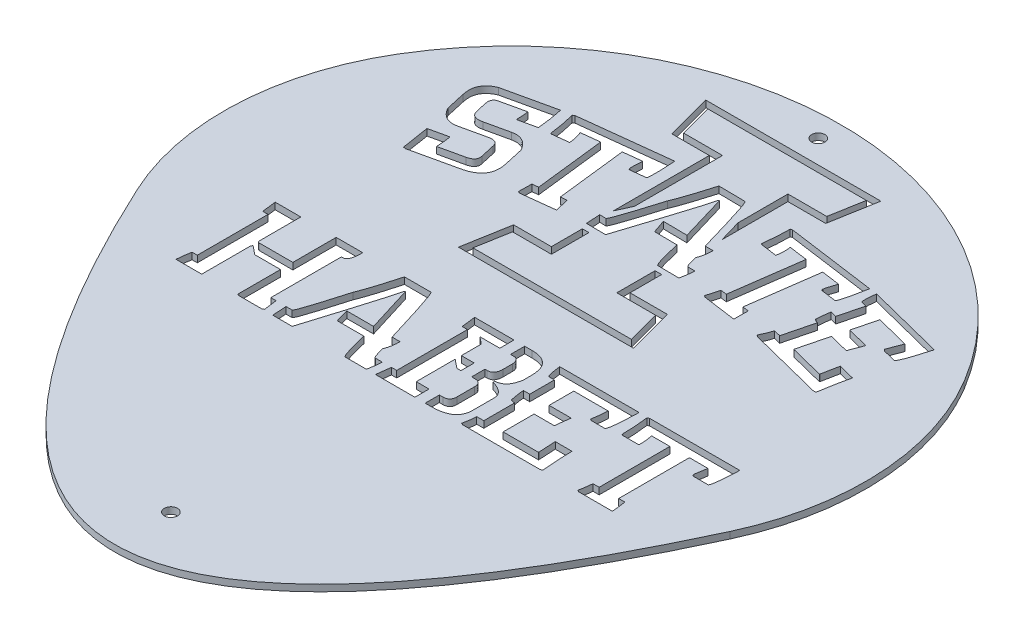
SolidWorks part; units mm, degrees
ref_plane "Front Plane" through (0, 0, 0) normal (0, 0, 1) x (1, 0, 0)
ref_plane "Top Plane" through (0, 0, 0) normal (0, 1, 0) x (1, 0, 0)
ref_plane "Right Plane" through (0, 0, 0) normal (1, 0, 0) x (0, 0, -1)
sketch "Sketch1" plane through (0, 0, 0) normal (0, 1, 0) x (1, 0, 0)
  arc A1 (105.41, 0) -> (-21.59, 0) centre (41.91, 0) ccw
  spline S0 degree 2 poles (-21.59, 0) (41.91, -152.4) (105.41, 0) knots 0 0 0 1 1 1
  dimension "D1" = 63.5
extrude "Boss-Extrude1" add sketch "Sketch1" along normal blind 1.27
fillet "Fillet1" radius 50.8 2 edges at (105.41, 0.635, 0) (-21.59, 0.635, 0)
sketch "Sketch2" plane through (0, 1.27, 0) normal (0, 1, 0) x (1, 0, 0)
  line L0 (-19.7843, 6.5271) -> (103.6043, 6.5271) construction
  line L1 (0.3218, -3.7763) -> (5.2567, -3.7763)
  line L2 (5.2567, -3.7763) -> (5.2567, -11.77)
  line L3 (5.5918, -12.105) -> (12.0561, -12.105)
  line L4 (12.0561, -12.105) -> (12.0561, -3.7763)
  line L5 (12.0561, -3.7763) -> (17.1645, -3.7763)
  line L6 (16.1396, -6.5039) -> (15.8085, -6.5039)
  line L7 (15.8085, -6.5039) -> (15.8085, -20.0987)
  line L8 (15.8085, -20.0987) -> (16.8176, -20.0987)
  line L9 (17.1645, -22.6529) -> (16.8176, -22.8263)
  line L10 (16.8176, -22.8263) -> (12.403, -22.8263)
  line L11 (12.0561, -22.4794) -> (12.0561, -14.4857)
  line L12 (12.0561, -14.4857) -> (7.1211, -14.4857)
  line L13 (7.1211, -14.4857) -> (5.4302, -13.1298)
  line L14 (5.4302, -13.1298) -> (5.2567, -13.4727)
  line L15 (5.2567, -13.4727) -> (5.2567, -22.8263)
  line L16 (5.2567, -22.8263) -> (0.3218, -22.8263)
  line L17 (0.6687, -20.0987) -> (1.6777, -20.0987)
  line L18 (1.6777, -20.0987) -> (1.6777, -6.5039)
  line L19 (1.6777, -6.5039) -> (0.6687, -6.5039)
  line L20 (25.2015, -3.7881) -> (30.298, -3.7881)
  line L21 (34.0347, -15.0021) -> (35.5641, -15.0021)
  line L22 (35.5641, -15.0021) -> (35.5641, -15.1755)
  line L23 (35.911, -20.1105) -> (37.2669, -20.1105)
  line L24 (36.924, -22.8263) -> (32.8522, -22.8263)
  line L25 (31.1494, -17.5563) -> (26.0529, -17.5563)
  line L26 (25.3631, -15.0021) -> (30.4715, -15.0021)
  line L27 (30.4715, -15.0021) -> (27.7439, -6.1689)
  line L28 (27.7439, -6.1689) -> (27.5822, -6.1689)
  line L29 (22.6473, -22.8263) -> (18.9106, -22.8263)
  line L30 (18.9106, -22.8263) -> (18.9106, -22.6529)
  line L31 (18.7372, -20.1105) -> (19.9197, -20.1105)
  line L32 (38.6662, -3.7763) -> (46.2361, -3.7763)
  line L33 (53.8061, -8.0333) -> (53.8061, -9.5626)
  line L34 (51.2519, -12.4479) -> (51.2519, -12.7948)
  line L35 (53.9795, -15.3371) -> (53.9795, -19.4207)
  line L36 (49.3875, -22.8263) -> (48.2132, -22.8263)
  line L37 (39.013, -20.0987) -> (40.0221, -20.0987)
  line L38 (40.0221, -20.0987) -> (40.0221, -6.5039)
  line L39 (40.0221, -6.5039) -> (39.013, -6.5039)
  line L40 (43.7746, -7.6864) -> (43.7746, -11.427)
  line L41 (43.7746, -11.427) -> (46.2361, -11.427)
  line L42 (50.0654, -9.7242) -> (50.0654, -7.8598)
  line L43 (49.214, -6.5039) -> (48.3, -6.5039)
  line L44 (43.7746, -12.6213) -> (43.7746, -20.0987)
  line L45 (43.7746, -20.0987) -> (46.2361, -20.0987)
  line L46 (50.227, -18.7427) -> (50.227, -15.3371)
  line L47 (48.8711, -13.9812) -> (48.3, -13.9812)
  line L48 (45.4655, -13.9812) -> (43.7746, -12.6213)
  line L49 (55.0634, -3.8157) -> (70.3373, -3.8157)
  line L50 (69.6554, -9.7637) -> (67.117, -9.7637)
  line L51 (67.117, -9.7637) -> (66.7701, -9.5902)
  line L52 (67.117, -6.5315) -> (60.4911, -6.5315)
  line L53 (60.4911, -6.5315) -> (60.4911, -11.2772)
  line L54 (60.4911, -11.2772) -> (64.7363, -11.2772)
  line L55 (64.4012, -14.1665) -> (60.4911, -14.1665)
  line L56 (60.4911, -14.1665) -> (60.4911, -20.1105)
  line L57 (60.4911, -20.1105) -> (67.2904, -20.1105)
  line L58 (67.2904, -20.1105) -> (67.2904, -19.941)
  line L59 (67.117, -16.7207) -> (70.3373, -16.7207)
  line L60 (70.6803, -22.6529) -> (70.3373, -22.8263)
  line L61 (70.3373, -22.8263) -> (55.4103, -22.8263)
  line L62 (55.4103, -22.8263) -> (55.0634, -22.6529)
  line L63 (55.4103, -20.1105) -> (56.7662, -20.1105)
  line L64 (56.7662, -20.1105) -> (56.7662, -14.1665)
  line L65 (55.568, -11.2772) -> (56.7662, -11.2772)
  line L66 (56.7662, -11.2772) -> (56.7662, -6.5315)
  line L67 (56.7662, -6.5315) -> (55.7414, -6.5315)
  line L68 (72.3121, -3.7763) -> (89.6593, -3.7763)
  line L69 (88.9813, -9.2158) -> (86.2537, -9.2158)
  line L70 (86.2537, -6.5039) -> (82.6865, -6.5039)
  line L71 (82.6865, -6.5039) -> (82.6865, -20.0987)
  line L72 (82.6865, -20.0987) -> (83.873, -20.0987)
  line L73 (84.2159, -22.8263) -> (77.7516, -22.8263)
  line L74 (77.7516, -22.8263) -> (77.4047, -22.6529)
  line L75 (77.7516, -20.0987) -> (78.938, -20.0987)
  line L76 (78.938, -20.0987) -> (78.938, -6.5039)
  line L77 (78.938, -6.5039) -> (75.3708, -6.5039)
  line L78 (75.7019, -9.2158) -> (72.6432, -9.2158)
  line L79 (71.9652, -3.9497) -> (72.3121, -3.7763)
  line L80 (46.2361, -6.5039) -> (42.4029, -6.5039)
  line L82 (46.2361, -20.0987) -> (46.2361, -22.8263)
  line L84 (48.2132, -20.0987) -> (48.2132, -22.8263)
  line L86 (48.3, -13.9812) -> (48.3, -11.427)
  line L88 (46.2361, -13.9812) -> (46.2361, -11.427)
  line L90 (48.3, -6.5039) -> (48.3, -3.7763)
  line L92 (46.2361, -6.5039) -> (46.2361, -3.7763)
  line L93 (48.3, -11.427) -> (48.6977, -11.427)
  line L94 (46.2361, -13.9812) -> (45.4655, -13.9812)
  line L95 (48.2132, -20.0987) -> (48.8711, -20.0987)
  line L96 (46.2361, -22.8263) -> (38.6662, -22.8263)
  line L97 (48.3, -3.7763) -> (49.7225, -3.7763)
  arc A0 (-12.5617, 32.6356) -> (-15.0576, -14.8714) centre (31.0157, 6.5271) ccw construction
  arc A1 (98.8776, -14.8714) -> (96.3817, 32.6356) centre (52.8043, 6.5271) ccw construction
  spline S0 degree 3 poles (5.2567, -11.77) (5.2767, -11.8548) (5.3249, -12.0461) (5.5115, -12.11) (5.5918, -12.105) knots 0 0 0 0 0.531818 1 1 1 1
  spline S1 degree 3 poles (17.1645, -3.7763) (17.1601, -4.1742) (17.1498, -4.7348) (17.0306, -5.4153) (16.9262, -5.8056) (16.7819, -6.1098) (16.5581, -6.4058) (16.3037, -6.5067) (16.1396, -6.5039) knots 0 0 0 0 0.377825 0.528227 0.653888 0.759096 0.845794 1 1 1 1
  spline S2 degree 3 poles (16.8176, -20.0987) (16.814, -20.2059) (16.8417, -20.3915) (16.8635, -20.6762) (16.9085, -20.9683) (16.9512, -21.3148) (17.0487, -21.8808) (17.1036, -22.3353) (17.1645, -22.6529) knots 0 0 0 0 0.124228 0.21791 0.332039 0.467782 0.624075 1 1 1 1
  spline S3 degree 3 poles (12.403, -22.8263) (12.318, -22.8238) (12.0973, -22.785) (12.0586, -22.5644) (12.0561, -22.4794) knots 0 0 0 0 0.5 1 1 1 1
  spline S4 degree 3 poles (0.3218, -22.8263) (0.3165, -22.6719) (0.3428, -22.4242) (0.367, -22.0674) (0.4109, -21.7462) (0.4547, -21.3854) (0.5491, -20.8333) (0.6074, -20.3977) (0.6687, -20.0987) knots 0 0 0 0 0.167857 0.271329 0.389634 0.521087 0.667537 1 1 1 1
  spline S5 degree 3 poles (0.6687, -6.5039) (0.6085, -6.144) (0.554, -5.6333) (0.4561, -5.0015) (0.4132, -4.6261) (0.3683, -4.3196) (0.3476, -4.0427) (0.3199, -3.8703) (0.3218, -3.7763) knots 0 0 0 0 0.397879 0.560026 0.697261 0.809965 0.897811 1 1 1 1
  spline S6 degree 3 poles (30.298, -3.7881) (30.3661, -3.8248) (30.4363, -3.9693) (30.5488, -4.2076) (30.6729, -4.5173) (30.8211, -4.9121) (31.001, -5.3927) (31.1939, -5.9635) (31.4172, -6.6196) (31.6586, -7.3647) (31.9339, -8.1958) (32.2222, -9.117) (32.5383, -10.1249) (32.8826, -11.2182) (33.3801, -12.8553) (33.7761, -14.1233) (34.0347, -15.0021) knots 0 0 0 0 0.018773 0.039327 0.067393 0.103006 0.146294 0.197354 0.255675 0.321893 0.395795 0.477496 0.566465 0.663438 0.767898 1 1 1 1
  spline S7 degree 3 poles (35.5641, -15.1755) (35.5648, -15.6483) (35.4856, -16.5757) (35.2298, -17.4708) (35.0596, -17.8913) knots 0 0 0 0 0.510454 1 1 1 1
  spline S8 degree 3 poles (35.0596, -17.8913) (35.1356, -18.2179) (35.265, -18.6679) (35.4319, -19.2222) (35.5425, -19.5348) (35.6415, -19.7812) (35.7482, -19.979) (35.8327, -20.0977) (35.911, -20.1105) knots 0 0 0 0 0.415941 0.581563 0.718283 0.827951 0.909707 1 1 1 1
  spline S9 degree 3 poles (37.2669, -20.1105) (37.2681, -20.2619) (37.2542, -20.5079) (37.2195, -20.8611) (37.1787, -21.1828) (37.1326, -21.5418) (37.0487, -22.094) (36.9742, -22.5255) (36.924, -22.8263) knots 0 0 0 0 0.165637 0.269704 0.388543 0.520588 0.666057 1 1 1 1
  spline S10 degree 3 poles (32.8522, -22.8263) (32.7974, -22.8218) (32.728, -22.7534) (32.646, -22.6308) (32.5693, -22.4841) (32.4826, -22.2993) (32.392, -22.0729) (32.2997, -21.8048) (32.1962, -21.4963) (32.0873, -21.1463) (31.9675, -20.7556) (31.8466, -20.3229) (31.7207, -19.8481) (31.5875, -19.3329) (31.39, -18.5657) (31.2491, -17.9676) (31.1494, -17.5563) knots 0 0 0 0 0.0276 0.04989 0.079536 0.116114 0.159439 0.210268 0.268221 0.333986 0.406901 0.487456 0.574996 0.670392 0.772966 1 1 1 1
  spline S11 degree 3 poles (26.0529, -17.5563) (25.9507, -17.2492) (25.803, -16.8139) (25.6343, -16.2609) (25.5398, -15.9174) (25.4647, -15.6218) (25.3956, -15.324) (25.3673, -15.1214) (25.3631, -15.0021) knots 0 0 0 0 0.366212 0.519992 0.654155 0.76917 0.86511 1 1 1 1
  spline S12 degree 3 poles (27.5822, -6.1689) (27.5828, -6.2184) (27.5635, -6.3058) (27.5384, -6.4429) (27.5002, -6.5892) (27.458, -6.7655) (27.4069, -6.9722) (27.3423, -7.2079) (27.2736, -7.4756) (27.1882, -7.7715) (27.1001, -8.0984) (26.995, -8.4534) (26.8863, -8.8405) (26.7635, -9.2564) (26.6327, -9.7029) (26.4967, -10.1795) (26.3445, -10.6843) (26.1893, -11.2202) (26.0173, -11.784) (25.8417, -12.3801) (25.6515, -13.0048) (25.4552, -13.6611) (25.2458, -14.3451) (25.0283, -15.0596) (24.8053, -15.8042) (24.5675, -16.5789) (24.3188, -17.3821) (24.0691, -18.2184) (23.797, -19.0792) (23.5278, -19.9756) (23.1441, -21.2281) (22.8431, -22.18) (22.6473, -22.8263) knots 0 0 0 0 0.008482 0.015422 0.024059 0.034567 0.046726 0.060811 0.076767 0.094434 0.113971 0.13522 0.158339 0.183391 0.210094 0.238665 0.268953 0.301108 0.33498 0.370721 0.408395 0.44772 0.488979 0.531889 0.576668 0.623164 0.671811 0.721826 0.773842 0.827659 0.88341 1 1 1 1
  spline S13 degree 3 poles (18.9106, -22.6529) (18.8851, -22.3323) (18.852, -21.8788) (18.8041, -21.3103) (18.7827, -20.9658) (18.7605, -20.6756) (18.7479, -20.397) (18.7397, -20.2143) (18.7372, -20.1105) knots 0 0 0 0 0.378522 0.535222 0.671642 0.784811 0.877726 1 1 1 1
  spline S14 degree 3 poles (19.9197, -20.1105) (19.9851, -20.0698) (20.0578, -19.9407) (20.163, -19.7297) (20.2745, -19.475) (20.3918, -19.1515) (20.5362, -18.7653) (20.6926, -18.3115) (20.8651, -17.7922) (21.0556, -17.2065) (21.2589, -16.5543) (21.4791, -15.8351) (21.7216, -15.0521) (21.9723, -14.1998) (22.3414, -12.9306) (22.6318, -11.9467) (22.8207, -11.2654) knots 0 0 0 0 0.02398 0.046649 0.076156 0.113186 0.157286 0.208717 0.26749 0.333211 0.40669 0.487124 0.575043 0.670203 0.772728 1 1 1 1
  spline S15 degree 3 poles (22.8207, -11.2654) (22.9937, -10.8713) (23.2405, -10.2161) (23.5681, -9.2626) (23.8563, -8.384) (24.1602, -7.3918) (24.6266, -5.8518) (24.9663, -4.6357) (25.2015, -3.7881) knots 0 0 0 0 0.16438 0.267414 0.385207 0.517635 0.663905 1 1 1 1
  spline S16 degree 3 poles (49.7225, -3.7763) (50.0428, -3.7745) (50.5096, -3.805) (51.1038, -3.9183) (51.5047, -4.0313) (51.8741, -4.1812) (52.2107, -4.3676) (52.5166, -4.5854) (52.7917, -4.8359) (53.0333, -5.1205) (53.2377, -5.4407) (53.4187, -5.7885) (53.5573, -6.1755) (53.6734, -6.5925) (53.7784, -7.2144) (53.8067, -7.6999) (53.8061, -8.0333) knots 0 0 0 0 0.141988 0.206643 0.267847 0.326362 0.382935 0.43805 0.49247 0.547434 0.603008 0.660577 0.72084 0.784848 0.852262 1 1 1 1
  spline S17 degree 3 poles (53.8061, -9.5626) (53.7298, -9.9914) (53.5818, -10.6017) (53.2325, -11.3128) (52.9356, -11.728) (52.587, -12.053) (52.0419, -12.366) (51.5697, -12.4538) (51.2519, -12.4479) knots 0 0 0 0 0.309204 0.44026 0.558794 0.668748 0.775024 1 1 1 1
  spline S18 degree 3 poles (51.2519, -12.7948) (51.6605, -12.9151) (52.2378, -13.1195) (52.9065, -13.5074) (53.2957, -13.8127) (53.6042, -14.1462) (53.8955, -14.6383) (53.9799, -15.0591) (53.9795, -15.3371) knots 0 0 0 0 0.318967 0.454552 0.576178 0.687424 0.792188 1 1 1 1
  spline S19 degree 3 poles (53.9795, -19.4207) (53.9753, -19.6869) (53.9498, -20.0798) (53.8269, -20.5756) (53.6987, -20.9111) (53.539, -21.2204) (53.3361, -21.4994) (53.1058, -21.7574) (52.8316, -21.9836) (52.5256, -22.1848) (52.1794, -22.3534) (51.8039, -22.5047) (51.3882, -22.6202) (50.9398, -22.7171) (50.2686, -22.7966) (49.7474, -22.8338) (49.3875, -22.8263) knots 0 0 0 0 0.122782 0.180144 0.234516 0.287818 0.339851 0.39295 0.446621 0.502992 0.561152 0.623604 0.689077 0.759544 0.834572 1 1 1 1
  spline S20 degree 3 poles (38.6662, -22.8263) (38.6643, -22.7322) (38.692, -22.5598) (38.7127, -22.283) (38.7576, -21.9764) (38.8005, -21.6011) (38.8984, -20.9693) (38.9529, -20.4586) (39.013, -20.0987) knots 0 0 0 0 0.102189 0.190035 0.302739 0.439974 0.602121 1 1 1 1
  spline S21 degree 3 poles (39.013, -6.5039) (38.9529, -6.144) (38.8984, -5.6333) (38.8005, -5.0015) (38.7576, -4.6261) (38.7127, -4.3196) (38.692, -4.0427) (38.6643, -3.8703) (38.6662, -3.7763) knots 0 0 0 0 0.397879 0.560026 0.697261 0.809965 0.897811 1 1 1 1
  spline S22 degree 3 poles (42.4029, -6.5039) (42.6032, -6.6581) (42.8861, -6.8721) (43.2248, -7.1508) (43.4196, -7.3116) (43.5694, -7.445) (43.6894, -7.5609) (43.7619, -7.6346) (43.7746, -7.6864) knots 0 0 0 0 0.416958 0.584812 0.72325 0.833736 0.914955 1 1 1 1
  spline S23 degree 3 poles (48.6977, -11.427) (48.8988, -11.4228) (49.2012, -11.3894) (49.5355, -11.1952) (49.7353, -11.005) (49.8856, -10.7568) (50.0347, -10.3315) (50.0693, -9.9745) (50.0654, -9.7242) knots 0 0 0 0 0.245182 0.352852 0.460208 0.573842 0.698393 1 1 1 1
  spline S24 degree 3 poles (50.0654, -7.8598) (50.0669, -7.7141) (50.0443, -7.4989) (49.9527, -7.2319) (49.8564, -7.0536) (49.7373, -6.889) (49.534, -6.6877) (49.3478, -6.57) (49.214, -6.5039) knots 0 0 0 0 0.257766 0.378193 0.496611 0.614573 0.73607 1 1 1 1
  spline S25 degree 3 poles (48.8711, -20.0987) (49.0734, -20.1057) (49.359, -20.0623) (49.7013, -19.9222) (49.8942, -19.7657) (50.0507, -19.5713) (50.1967, -19.2309) (50.2299, -18.9423) (50.227, -18.7427) knots 0 0 0 0 0.274588 0.390158 0.499896 0.609633 0.72757 1 1 1 1
  spline S26 degree 3 poles (50.227, -15.3371) (50.2277, -15.1371) (50.1995, -14.8464) (50.0495, -14.5079) (49.8944, -14.3138) (49.7003, -14.1588) (49.3618, -14.0088) (49.0712, -13.9805) (48.8711, -13.9812) knots 0 0 0 0 0.274057 0.390311 0.5 0.609689 0.725943 1 1 1 1
  spline S27 degree 3 poles (70.3373, -3.8157) (70.3212, -4.2808) (70.3024, -4.9551) (70.2641, -5.8221) (70.2332, -6.403) (70.1965, -6.9376) (70.1631, -7.4266) (70.1222, -7.8679) (70.0847, -8.2624) (70.041, -8.6107) (69.9956, -8.9134) (69.9435, -9.1694) (69.8952, -9.3796) (69.8404, -9.5424) (69.778, -9.6803) (69.7141, -9.7597) (69.6554, -9.7637) knots 0 0 0 0 0.230352 0.333856 0.429597 0.518237 0.599091 0.672218 0.737577 0.795252 0.845932 0.889041 0.924531 0.952707 0.973649 1 1 1 1
  spline S28 degree 3 poles (66.7701, -9.5902) (66.8245, -9.232) (66.897, -8.7211) (66.9825, -8.0731) (67.0278, -7.6654) (67.0696, -7.3084) (67.1029, -6.9367) (67.118, -6.6829) (67.117, -6.5315) knots 0 0 0 0 0.352909 0.50259 0.636562 0.752444 0.852662 1 1 1 1
  spline S29 degree 3 poles (64.7363, -11.2772) (64.683, -11.6248) (64.6182, -12.1206) (64.5329, -12.7445) (64.4846, -13.1321) (64.4506, -13.4661) (64.4151, -13.8045) (64.4008, -14.0322) (64.4012, -14.1665) knots 0 0 0 0 0.362431 0.515491 0.649224 0.765001 0.861638 1 1 1 1
  spline S30 degree 3 poles (67.2904, -19.941) (67.2651, -19.5363) (67.2316, -18.9634) (67.1841, -18.2449) (67.1622, -17.8072) (67.1405, -17.4382) (67.1277, -17.0833) (67.1194, -16.8521) (67.117, -16.7207) knots 0 0 0 0 0.377135 0.533875 0.669731 0.784774 0.877729 1 1 1 1
  spline S31 degree 3 poles (70.3373, -16.7207) (70.3359, -17.1281) (70.3479, -17.7616) (70.3835, -18.6352) (70.4243, -19.3551) (70.4708, -20.1187) (70.5519, -21.2227) (70.6293, -22.0722) (70.6803, -22.6529) knots 0 0 0 0 0.205603 0.319754 0.441286 0.569516 0.705819 1 1 1 1
  spline S32 degree 3 poles (55.0634, -22.6529) (55.1707, -22.1744) (55.3209, -21.3308) (55.4133, -20.4779) (55.4103, -20.1105) knots 0 0 0 0 0.572014 1 1 1 1
  spline S33 degree 3 poles (56.7662, -14.1665) (56.6425, -14.1677) (56.4675, -14.1617) (56.2547, -14.1237) (56.1326, -14.0884) (56.0351, -14.0447) (55.9504, -13.9621) (55.9075, -13.8884) (55.9148, -13.8314) knots 0 0 0 0 0.371737 0.524226 0.647832 0.753726 0.840279 1 1 1 1
  spline S34 degree 3 poles (55.9148, -13.8314) (55.853, -13.5404) (55.797, -13.1189) (55.7009, -12.5881) (55.6576, -12.2482) (55.6132, -11.9494) (55.5901, -11.6294) (55.5628, -11.4107) (55.568, -11.2772) knots 0 0 0 0 0.345623 0.494312 0.626973 0.744084 0.845332 1 1 1 1
  spline S35 degree 3 poles (55.7414, -6.5315) (55.6537, -6.5126) (55.5723, -6.366) (55.4756, -6.1275) (55.3982, -5.8258) (55.3096, -5.4447) (55.1971, -4.7642) (55.1114, -4.2128) (55.0634, -3.8157) knots 0 0 0 0 0.085765 0.166449 0.274219 0.411848 0.579054 1 1 1 1
  spline S36 degree 3 poles (89.6593, -3.7763) (89.6381, -4.2006) (89.6122, -4.8173) (89.562, -5.6105) (89.5265, -6.1427) (89.4926, -6.6317) (89.4523, -7.0769) (89.4127, -7.4803) (89.3749, -7.842) (89.3322, -8.1615) (89.2847, -8.4373) (89.2377, -8.6715) (89.192, -8.8623) (89.1464, -9.0135) (89.087, -9.1362) (89.0358, -9.2144) (88.9813, -9.2158) knots 0 0 0 0 0.229959 0.333973 0.430181 0.518586 0.599251 0.672128 0.737933 0.796058 0.84656 0.889372 0.925244 0.952903 0.974211 1 1 1 1
  spline S37 degree 3 poles (86.2537, -9.2158) (86.1669, -9.2187) (85.9557, -9.1768) (85.9056, -8.9689) (85.9069, -8.8847) knots 0 0 0 0 0.509252 1 1 1 1
  spline S38 degree 3 poles (85.9069, -8.8847) (85.9019, -8.7564) (85.9284, -8.5482) (85.9524, -8.244) (85.9956, -7.9648) (86.0404, -7.6487) (86.135, -7.1599) (86.1929, -6.7713) (86.2537, -6.5039) knots 0 0 0 0 0.159143 0.261079 0.380037 0.510802 0.658785 1 1 1 1
  spline S39 degree 3 poles (83.873, -20.0987) (83.9209, -20.4603) (83.9941, -20.9682) (84.0799, -21.6015) (84.1257, -21.9763) (84.1667, -22.2834) (84.1982, -22.5591) (84.2153, -22.7326) (84.2159, -22.8263) knots 0 0 0 0 0.397951 0.559933 0.697195 0.809921 0.897937 1 1 1 1
  spline S40 degree 3 poles (77.4047, -22.6529) (77.4585, -22.334) (77.5304, -21.8822) (77.6163, -21.3144) (77.6618, -20.9684) (77.7033, -20.6758) (77.7358, -20.3922) (77.7521, -20.2055) (77.7516, -20.0987) knots 0 0 0 0 0.37615 0.532208 0.66795 0.782077 0.87592 1 1 1 1
  spline S41 degree 3 poles (75.3708, -6.5039) (75.5002, -6.8751) (75.667, -7.7777) (75.703, -8.6933) (75.7019, -9.2158) knots 0 0 0 0 0.428461 1 1 1 1
  spline S42 degree 3 poles (72.6432, -9.2158) (72.5571, -9.2223) (72.3584, -9.1694) (72.3055, -8.9707) (72.3121, -8.8847) knots 0 0 0 0 0.5 1 1 1 1
  spline S43 degree 3 poles (72.3121, -8.8847) (72.3172, -8.0822) (72.2442, -6.4328) (72.083, -4.7898) (71.9652, -3.9497) knots 0 0 0 0 0.486078 1 1 1 1
  dimension "D1" = 2.0638
  dimension "D2" = 1.9771
  dimension "D3" = 2.4616
extrude "HABET text" cut sketch "Sketch2" against normal blind 2.54
sketch "Sketch3" plane through (0, 1.27, 0) normal (0, 1, 0) x (1, 0, 0)
  arc A0 (-12.5617, 32.6356) -> (-15.0576, -14.8714) centre (31.0157, 6.5271) ccw construction
  arc A1 (98.8776, -14.8714) -> (96.3817, 32.6356) centre (52.8043, 6.5271) ccw construction
  spline S0 degree 2 poles (-19.7144, 9.1923) (41.91, 36.5277) (103.5344, 9.1923) knots 0 0 0 1 1 1 construction
  text T0 " STATE" font "NCAA Iowa St Cyclone" height 19.05
  point P5 (41.91, 0)
  point P15 (-19.7144, 9.1923)
  point P18 (103.5344, 9.1923)
  dimension "D1" = 22.86
extrude "State Logo 1" cut sketch "Sketch3" against normal blind 2.54
sketch "Sketch4" plane through (0, 1.27, 0) normal (0, 1, 0) x (1, 0, 0)
  line L0 (26.95, 7.62) -> (57.43, 7.62)
  line L23 (35.56, 14.0941) -> (48.26, 46.8659) construction
  line L24 (34.29, 15.3641) -> (27.0259, 15.3641)
  line L25 (27.0259, 15.3641) -> (25.4364, 6.35)
  line L27 (57.43, 7.62) -> (55.7285, 13.97)
  line L29 (55.7285, 13.97) -> (48.26, 13.97)
  line L31 (48.26, 13.97) -> (48.26, 21.316)
  line L33 (48.26, 46.8659) -> (55.7285, 46.8659)
  line L34 (55.7285, 46.8659) -> (56.87, 53.34)
  line L35 (56.87, 53.34) -> (26.39, 53.34)
  line L37 (35.56, 46.99) -> (35.56, 30.0693)
  line L38 (35.56, 14.0941) -> (28.0915, 14.0941)
  line L39 (28.0915, 14.0941) -> (26.95, 7.62)
  line L40 (35.56, 46.99) -> (28.0915, 46.99)
  line L41 (28.0915, 46.99) -> (26.39, 53.34)
  line L42 (25.4364, 6.35) -> (59.0851, 6.35)
  line L43 (59.0851, 6.35) -> (56.703, 15.24)
  line L44 (56.703, 15.24) -> (49.53, 15.24)
  line L45 (49.53, 15.24) -> (49.53, 21.316)
  line L46 (49.53, 45.5959) -> (56.7941, 45.5959)
  line L47 (56.7941, 45.5959) -> (58.3836, 54.61)
  line L48 (58.3836, 54.61) -> (24.7349, 54.61)
  line L49 (27.117, 45.72) -> (24.7349, 54.61)
  line L50 (34.29, 45.72) -> (27.117, 45.72)
  line L51 (34.29, 45.72) -> (34.29, 27.2574)
  line L52 (35.56, 15.3641) -> (27.0259, 15.3641) construction
  line L53 (48.26, 21.316) -> (49.53, 21.316)
  line L54 (34.29, 21.316) -> (35.56, 21.316)
  line L55 (35.56, 30.0693) -> (34.29, 27.2574)
  line L57 (48.26, 32.7297) -> (48.9825, 30.2498) construction
  line L58 (49.53, 32.9109) -> (49.53, 45.5959)
  line L59 (49.53, 32.9109) -> (48.26, 37.2701)
  line L60 (35.56, 21.316) -> (35.56, 14.0941)
  line L61 (35.56, 46.99) -> (35.56, 14.0941) construction
  line L62 (34.29, 21.316) -> (34.29, 15.3641)
  line L63 (34.29, 45.72) -> (34.29, 14.0941) construction
  line L64 (49.53, 15.24) -> (49.53, 46.8659) construction
  line L65 (48.26, 37.2701) -> (48.26, 46.8659)
  line L66 (48.26, 13.97) -> (48.26, 46.8659) construction
  line L67 (48.26, 45.5959) -> (56.7941, 45.5959) construction
  line L68 (35.56, 30.0693) -> (35.56, 21.316) construction
  line L69 (34.29, 27.2574) -> (34.29, 21.316) construction
  line L70 (49.53, 32.9109) -> (49.53, 21.316) construction
  line L71 (48.26, 37.2701) -> (48.26, 21.316) construction
  line L72 (34.8044, 25.3109) -> (35.56, 26.9839) construction
  line L73 (35.56, 30.0693) -> (35.56, 21.316) construction
  line L75 (37.5005, 22.5636) -> (33.7638, 22.6069) construction
  spline S0 degree 3 poles (45.3838, 41.5072) (45.4032, 41.4936) (45.4656, 41.4501) (45.5294, 41.301) (45.6307, 41.084) (45.7499, 40.7736) (45.8963, 40.3788) (46.065, 39.8952) (46.2526, 39.3227) (46.4665, 38.6635) (46.7015, 37.9154) (46.963, 37.0806) (47.2407, 36.1554) (47.5498, 35.145) (47.8766, 34.0452) (48.2211, 32.8573) (48.5989, 31.5846) (48.8518, 30.7046) (48.9825, 30.2498) knots 0 0 0 0 0.005928 0.019061 0.039478 0.067423 0.102922 0.146303 0.197155 0.255589 0.321925 0.395848 0.477262 0.566679 0.663591 0.767999 0.880091 1 1 1 1 construction
  spline S2 degree 3 poles (34.8044, 25.3109) (34.8264, 25.3284) (34.8857, 25.3756) (34.9583, 25.5038) (35.0522, 25.6892) (35.1669, 25.9411) (35.2888, 26.2636) (35.4415, 26.646) (35.6006, 27.1) (35.7834, 27.6162) (35.973, 28.2035) (36.1931, 28.8501) (36.4197, 29.5677) (36.6682, 30.349) (36.9324, 31.1978) (37.2124, 32.1122) (37.507, 33.0944) (37.7106, 33.771) (37.8158, 34.1205) knots 0 0 0 0 0.008979 0.024207 0.046495 0.07617 0.112953 0.157345 0.208511 0.267548 0.333392 0.406847 0.48712 0.575277 0.670388 0.772856 0.882686 1 1 1 1 construction
  point P2 (41.91, 0)
  point P3 (41.91, 30.48)
  dimension "D1" = 75
  dimension "D2" = 80
  dimension "D3" = 6.35
  dimension "D4" = 12.7
  dimension "D5" = 45.72
  dimension "D6" = 30.48
  dimension "D7" = 30.48
  dimension "D8" = 1.27
  dimension "D10" = 1.27
  dimension "D11" = 1.27
  dimension "D12" = 16.9207
  dimension "D13" = 7.4685
  dimension "D14" = 18.4626
  dimension "D9" = 1.27
extrude "State Logo 2" cut sketch "Sketch4" against normal blind 2.54
sketch "Sketch5" plane through (0, 1.27, 0) normal (0, 1, 0) x (1, 0, 0)
  line L0 (-19.7843, 6.5271) -> (103.6043, 6.5271) construction
  line L1 (41.91, 60.325) -> (41.91, 63.5) construction
  circle A0 centre (41.91, 59.055) radius 1.27
  circle A1 centre (41.91, -65.405) radius 1.27
  arc A2 (-12.5617, 32.6356) -> (-15.0576, -14.8714) centre (31.0157, 6.5271) ccw construction
  arc A3 (98.8776, -14.8714) -> (96.3817, 32.6356) centre (52.8043, 6.5271) ccw construction
  arc A4 (96.3817, 32.6356) -> (-12.5617, 32.6356) centre (41.91, 0) ccw construction
  point P4 (41.91, 6.5271)
  dimension "D1" = 2.54
  dimension "D3" = 124.46
  dimension "D2" = 3.175
extrude "Mount Holes" cut sketch "Sketch5" against normal blind 2.54
sketch "Sketch6" plane through (0, 1.27, 0) normal (0, 1, 0) x (1, 0, 0)
  line L0 (40.3109, 30.3562) -> (40.8297, 30.3498)
  line L1 (40.3109, 30.3562) -> (45.4192, 30.2932) construction
  line L2 (40.8297, 30.3498) -> (41.719, 27.7815)
  line L3 (46.0657, 27.7311) -> (40.9691, 27.7902) construction
  line L4 (41.719, 27.7815) -> (40.9691, 27.7902)
  spline S0 degree 3 poles (-1834.5321, -665.1974) (69.1352, -18.9287) (48.6954, 2.7966) (40.6844, 28.701) (40.5719, 29.0931) (40.4739, 29.4375) (40.4042, 29.7353) (40.3526, 29.9848) (39.5365, 34.449) (63.6979, 41.22) (-1951.6957, -147.3687) knots -30.117623 -30.117623 -30.117623 -30.117623 0.192989 0.365344 0.519928 0.653918 0.769874 0.865378 0.942022 5.884282 5.884282 5.884282 5.884282 only from (40.9691, 27.7902) to (40.3109, 30.3562) construction
  spline S1 degree 3 poles (40.9691, 27.7902) (40.9177, 27.9531) (40.8204, 28.2614) (40.6844, 28.701) (40.5719, 29.0931) (40.4739, 29.4375) (40.4042, 29.7353) (40.3526, 29.9848) (40.3159, 30.1857) (40.3124, 30.3049) (40.3109, 30.3562) knots 0 0 0 0 0.192989 0.365344 0.519928 0.653918 0.769874 0.865378 0.942022 1 1 1 1
extrude "Letter Touchups" add sketch "Sketch6" against normal up to surface (1.27 mm away) up to face at (41.91, 0, -60.325)
ref_plane "Plane1" through (41.91, 0, 0) normal (1, 0, 0) x (0, 0, -1)
